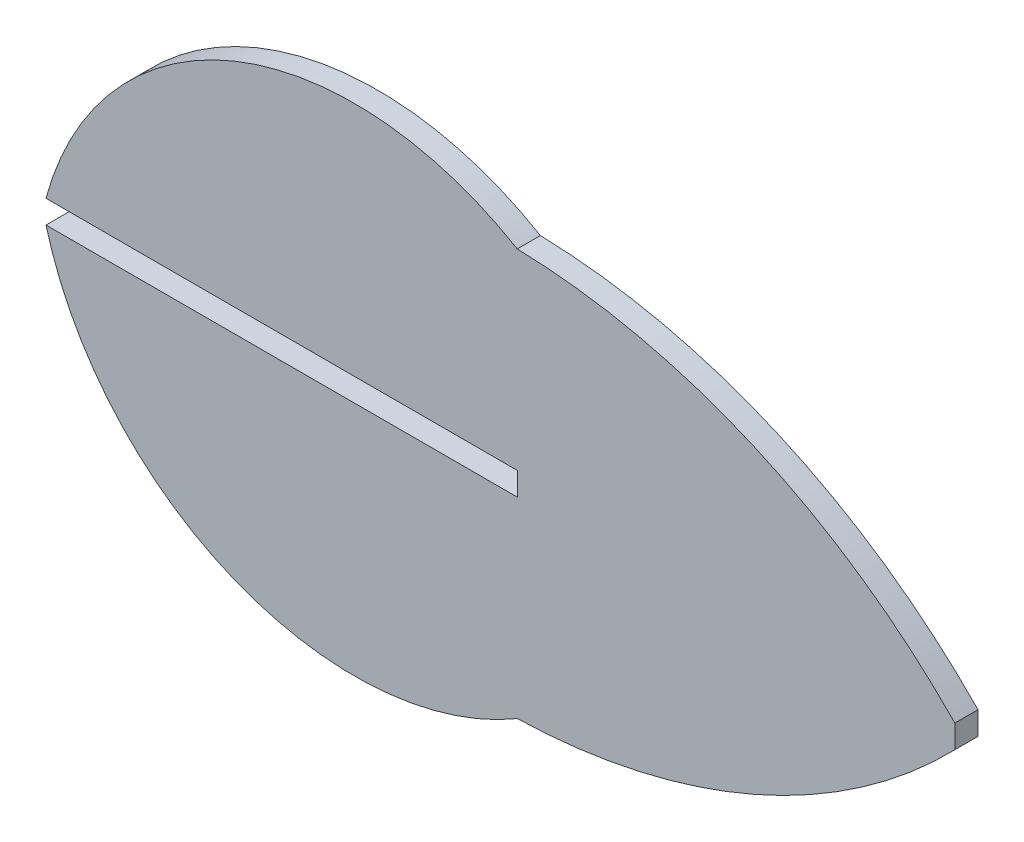
SolidWorks part; units mm, degrees
ref_plane "Front Plane" through (0, 0, 0) normal (0, 0, 1) x (1, 0, 0)
ref_plane "Top Plane" through (0, 0, 0) normal (0, 1, 0) x (1, 0, 0)
ref_plane "Right Plane" through (0, 0, 0) normal (1, 0, 0) x (0, 0, -1)
sketch "Sketch1" plane through (0, 0, 0) normal (0, 0, 1) x (1, 0, 0)
  line L0 (82.4447, -1.524) -> (82.4447, 0)
  line L2 (82.4447, 0) -> (51.4035, 0)
  line L5 (111.2695, -1.524) -> (111.2695, 0)
  line L6 (82.4447, -1.524) -> (51.4035, -1.524)
  arc A0 (82.4447, 12.6342) -> (111.2695, 0) centre (81.3365, -29.0931) cw
  arc A1 (51.4035, 0) -> (82.4447, 12.6342) centre (71.7207, -5.468) cw
  arc A2 (51.4035, -1.524) -> (82.4447, -14.1582) centre (71.7207, 3.944) ccw
  arc A3 (82.4447, -14.1582) -> (111.2695, -1.524) centre (81.3365, 27.5691) ccw
extrude "Boss-Extrude1" add sketch "Sketch1" along normal blind 1.524 contours L5 A0 A1 L2 L0 L6 A2 A3
